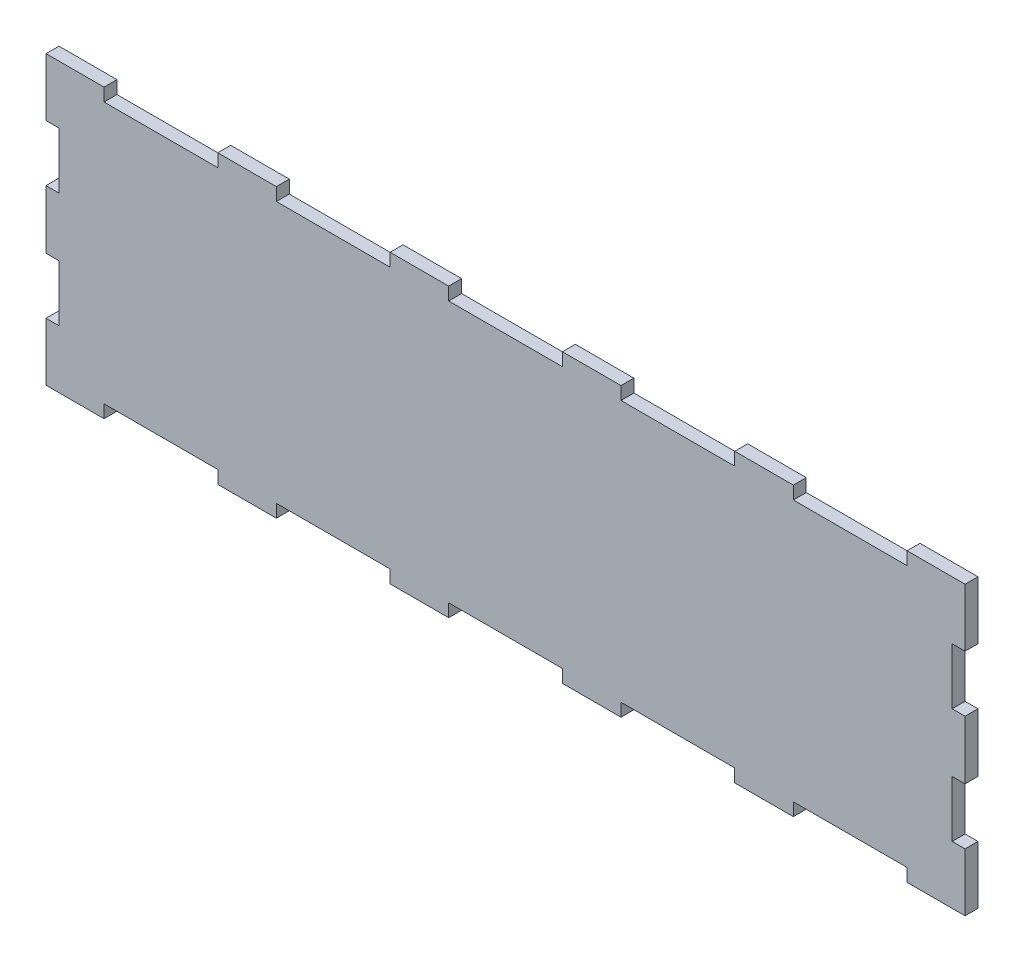
SolidWorks part; units mm, degrees
ref_plane "Front Plane" through (0, 0, 0) normal (0, 0, 1) x (1, 0, 0)
ref_plane "Top Plane" through (0, 0, 0) normal (0, 1, 0) x (1, 0, 0)
ref_plane "Right Plane" through (0, 0, 0) normal (1, 0, 0) x (0, 0, -1)
sketch "Sketch1" plane through (0, 0, 0) normal (0, 0, 1) x (1, 0, 0)
  line L1 (-203.2, -63.5) -> (203.2, -63.5)
  line L2 (-203.2, -63.5) -> (-203.2, 63.5)
  line L3 (-203.2, 63.5) -> (203.2, 63.5)
  line L4 (203.2, -63.5) -> (203.2, 63.5)
  line L5 (-203.2, -63.5) -> (203.2, 63.5) construction
  line L6 (-203.2, 63.5) -> (203.2, -63.5) construction
  point P0 (0, 0)
  dimension "D1" = 406.4
  dimension "D2" = 127
extrude "Boss-Extrude1" add sketch "Sketch1" along normal blind 5.715
sketch "Sketch2" plane through (0, 0, 5.715) normal (0, 0, 1) x (1, 0, 0)
  line L0 (-177.8, 57.785) -> (-127, 57.785)
  line L1 (-203.2, 63.5) -> (-177.8, 63.5) construction
  line L2 (-203.2, 63.5) -> (-203.2, 57.785) construction
  line L3 (-203.2, 57.785) -> (-177.8, 57.785) construction
  line L4 (-177.8, 63.5) -> (-177.8, 57.785)
  line L5 (-127, 57.785) -> (-127, 63.5)
  line L6 (203.2, 63.5) -> (-203.2, 63.5) construction
  line L7 (-127, 63.5) -> (-177.8, 63.5)
  line L9 (-50.8, 63.5) -> (-101.6, 63.5)
  line L10 (-101.6, 63.5) -> (-101.6, 57.785)
  line L11 (-101.6, 57.785) -> (-50.8, 57.785)
  line L12 (-50.8, 57.785) -> (-50.8, 63.5)
  line L13 (25.4, 63.5) -> (-25.4, 63.5)
  line L14 (-25.4, 63.5) -> (-25.4, 57.785)
  line L15 (-25.4, 57.785) -> (25.4, 57.785)
  line L16 (25.4, 57.785) -> (25.4, 63.5)
  line L17 (101.6, 63.5) -> (50.8, 63.5)
  line L18 (50.8, 63.5) -> (50.8, 57.785)
  line L19 (50.8, 57.785) -> (101.6, 57.785)
  line L20 (101.6, 57.785) -> (101.6, 63.5)
  line L21 (177.8, 63.5) -> (127, 63.5)
  line L22 (127, 63.5) -> (127, 57.785)
  line L23 (127, 57.785) -> (177.8, 57.785)
  line L24 (177.8, 57.785) -> (177.8, 63.5)
  dimension "D1" = 25.4
  dimension "D2" = 5.715
  dimension "D3" = 50.8
  dimension "D4" = 5
  dimension "D5" = 25.4
extrude "Top Jigsaw" cut sketch "Sketch2" against normal through all
mirror "Bottom Jigsaw" about plane through (0, 0, 0) normal (0, 1, 0) of "Top Jigsaw"
sketch "Sketch3" plane through (0, 0, 5.715) normal (0, 0, 1) x (1, 0, 0)
  line L0 (203.2, -63.5) -> (203.2, 63.5) construction
  line L1 (203.2, 38.1) -> (197.485, 38.1)
  line L2 (203.2, 38.1) -> (203.2, 12.7)
  line L3 (203.2, 12.7) -> (197.485, 12.7)
  line L4 (197.485, 38.1) -> (197.485, 12.7)
  line L5 (197.485, 38.1) -> (197.485, 63.5) construction
  line L6 (203.2, -12.7) -> (197.485, -12.7)
  line L7 (203.2, -12.7) -> (203.2, -38.1)
  line L8 (203.2, -38.1) -> (197.485, -38.1)
  line L9 (197.485, -12.7) -> (197.485, -38.1)
  line L10 (203.2, 63.5) -> (177.8, 63.5) construction
  line L11 (197.485, -12.7) -> (197.485, 12.7) construction
  line L12 (197.485, -38.1) -> (197.485, -63.5) construction
  line L13 (177.8, -63.5) -> (203.2, -63.5) construction
  dimension "D1" = 25.4
  dimension "D2" = 25.4
  dimension "D3" = 25.4
  dimension "D4" = 5.715
extrude "Right Jigsaw" cut sketch "Sketch3" against normal through all
mirror "Mirror2" about plane through (0, 0, 0) normal (1, 0, 0) of "Right Jigsaw"
sketch "Sketch4" plane through (0, 0, 5.715) normal (0, 0, 1) x (1, 0, 0)
  line L1 (-177.8, 57.785) -> (-127, 57.785) construction
  line L2 (-177.8, 63.5) -> (-177.546, 63.5)
  line L3 (-177.8, 63.5) -> (-177.8, 57.785)
  line L4 (-177.8, 57.785) -> (-177.546, 57.785)
  line L5 (-177.546, 63.5) -> (-177.546, 57.785)
  line L6 (-101.6, 57.785) -> (-50.8, 57.785) construction
  line L7 (-127, 63.5) -> (-127.254, 63.5)
  line L8 (-127, 63.5) -> (-127, 57.785)
  line L9 (-127, 57.785) -> (-127.254, 57.785)
  line L10 (-127.254, 63.5) -> (-127.254, 57.785)
  line L11 (-101.6, 63.5) -> (-101.346, 63.5)
  line L12 (-101.6, 63.5) -> (-101.6, 57.785)
  line L13 (-101.6, 57.785) -> (-101.346, 57.785)
  line L14 (-101.346, 63.5) -> (-101.346, 57.785)
  line L15 (-25.4, 57.785) -> (25.4, 57.785) construction
  line L16 (-50.8, 63.5) -> (-51.054, 63.5)
  line L17 (-50.8, 63.5) -> (-50.8, 57.785)
  line L18 (-50.8, 57.785) -> (-51.054, 57.785)
  line L19 (-51.054, 63.5) -> (-51.054, 57.785)
  line L20 (-25.4, 63.5) -> (-25.146, 63.5)
  line L21 (-25.4, 63.5) -> (-25.4, 57.785)
  line L22 (-25.4, 57.785) -> (-25.146, 57.785)
  line L23 (-25.146, 63.5) -> (-25.146, 57.785)
  line L24 (50.8, 57.785) -> (101.6, 57.785) construction
  line L25 (25.4, 63.5) -> (25.146, 63.5)
  line L26 (25.4, 63.5) -> (25.4, 57.785)
  line L27 (25.4, 57.785) -> (25.146, 57.785)
  line L28 (25.146, 63.5) -> (25.146, 57.785)
  line L29 (50.8, 63.5) -> (51.054, 63.5)
  line L30 (50.8, 63.5) -> (50.8, 57.785)
  line L31 (50.8, 57.785) -> (51.054, 57.785)
  line L32 (51.054, 63.5) -> (51.054, 57.785)
  line L33 (127, 57.785) -> (177.8, 57.785) construction
  line L34 (101.6, 63.5) -> (101.346, 63.5)
  line L35 (101.6, 63.5) -> (101.6, 57.785)
  line L36 (101.6, 57.785) -> (101.346, 57.785)
  line L37 (101.346, 63.5) -> (101.346, 57.785)
  line L38 (127, 63.5) -> (127.254, 63.5)
  line L39 (127, 63.5) -> (127, 57.785)
  line L40 (127, 57.785) -> (127.254, 57.785)
  line L41 (127.254, 63.5) -> (127.254, 57.785)
  line L42 (197.485, 38.1) -> (197.485, 12.7) construction
  line L43 (177.8, 63.5) -> (177.546, 63.5)
  line L44 (177.8, 63.5) -> (177.8, 57.785)
  line L45 (177.8, 57.785) -> (177.546, 57.785)
  line L46 (177.546, 63.5) -> (177.546, 57.785)
  line L47 (203.2, 38.1) -> (197.485, 38.1)
  line L48 (203.2, 38.1) -> (203.2, 37.846)
  line L49 (203.2, 37.846) -> (197.485, 37.846)
  line L50 (197.485, 38.1) -> (197.485, 37.846)
  line L51 (-197.485, 38.1) -> (-197.485, 12.7) construction
  line L52 (203.2, 12.7) -> (197.485, 12.7)
  line L53 (203.2, 12.7) -> (203.2, 12.954)
  line L54 (203.2, 12.954) -> (197.485, 12.954)
  line L55 (197.485, 12.7) -> (197.485, 12.954)
  line L56 (-203.2, 38.1) -> (-197.485, 38.1)
  line L57 (-203.2, 38.1) -> (-203.2, 37.846)
  line L58 (-203.2, 37.846) -> (-197.485, 37.846)
  line L59 (-197.485, 38.1) -> (-197.485, 37.846)
  line L61 (-203.2, 12.7) -> (-197.485, 12.7)
  line L62 (-203.2, 12.7) -> (-203.2, 12.954)
  line L63 (-203.2, 12.954) -> (-197.485, 12.954)
  line L64 (-197.485, 12.7) -> (-197.485, 12.954)
  dimension "D1" = 0.254
extrude "Boss-Extrude2" add sketch "Sketch4" against normal up to surface (5.715 mm away) up to face at (0, 0, 0)
mirror "Mirror3" about plane through (0, 0, 0) normal (0, 1, 0) of "Boss-Extrude2"
sketch "Sketch5" [suppressed] plane through (0, 0, 0) normal (0, 0, -1) x (-1, 0, 0)
  line L0 (0, 0) -> (-25.4, 0) construction
  line L1 (-172.085, 32.385) -> (-25.4, 32.385)
  line L2 (-172.085, 32.385) -> (-172.085, -32.385)
  line L3 (-172.085, -32.385) -> (-25.4, -32.385)
  line L4 (-25.4, 32.385) -> (-25.4, -32.385)
  line L5 (-197.485, 37.846) -> (-197.485, 12.954) construction
  line L6 (-51.054, 57.785) -> (-101.346, 57.785) construction
  dimension "D1" = 25.4
  dimension "D2" = 25.4
  dimension "D3" = 25.4
extrude "Cut-Extrude1" [suppressed] cut sketch "Sketch5" against normal through all
mirror "Mirror4" [suppressed] about plane through (0, 0, 0) normal (1, 0, 0)
fillet "Fillet1" [suppressed] radius 12.7
